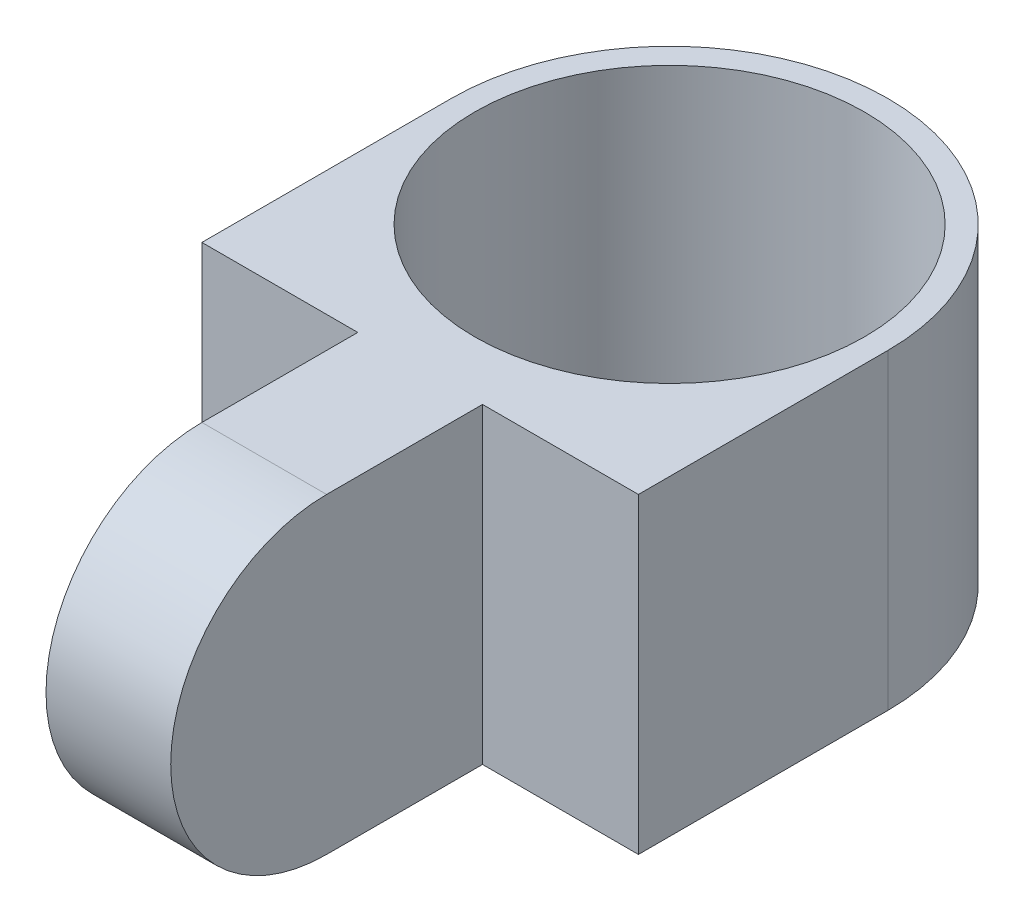
SolidWorks part; units mm, degrees
ref_plane "Front Plane" through (0, 0, 0) normal (0, 0, 1) x (1, 0, 0)
ref_plane "Top Plane" through (0, 0, 0) normal (0, 1, 0) x (1, 0, 0)
ref_plane "Right Plane" through (0, 0, 0) normal (1, 0, 0) x (0, 0, -1)
sketch "Sketch1" plane through (0, 0, 0) normal (0, 1, 0) x (1, 0, 0)
  circle A0 centre (0, 0) radius 6.25
  circle A1 centre (0, 0) radius 7
  dimension "D1" = 12.5
  dimension "D2" = 14
extrude "Boss-Extrude1" add sketch "Sketch1" along normal blind 10
sketch "Sketch3" plane through (0, 0, 0) normal (0, 0, 1) x (1, 0, 0)
  line L1 (-7, 10) -> (7, 10)
  line L2 (-7, 10) -> (-7, 0)
  line L3 (-7, 0) -> (7, 0)
  line L4 (7, 10) -> (7, 0)
extrude "Boss-Extrude2" add sketch "Sketch3" along normal blind 8
sketch "Sketch4" plane through (0, 10, 0) normal (0, 1, 0) x (1, 0, 0)
  line L0 (6.25, 0) -> (-6.25, 0) construction
  circle A0 centre (0, 0) radius 6.25
extrude "Cut-Extrude1" cut sketch "Sketch4" against normal blind 20
sketch "Sketch6" plane through (0, 0, 0) normal (1, 0, 0) x (0, 0, -1)
  line L3 (-8, 10) -> (-13, 10)
  line L4 (-8, 10) -> (-8, 0)
  line L5 (-8, 0) -> (-13, 0)
  arc A1 (-13, 10) -> (-13, 0) centre (-13, 5) ccw
  dimension "D1" = 5
extrude "Boss-Extrude3" add sketch "Sketch6" along normal blind 2 and the other way blind 2
